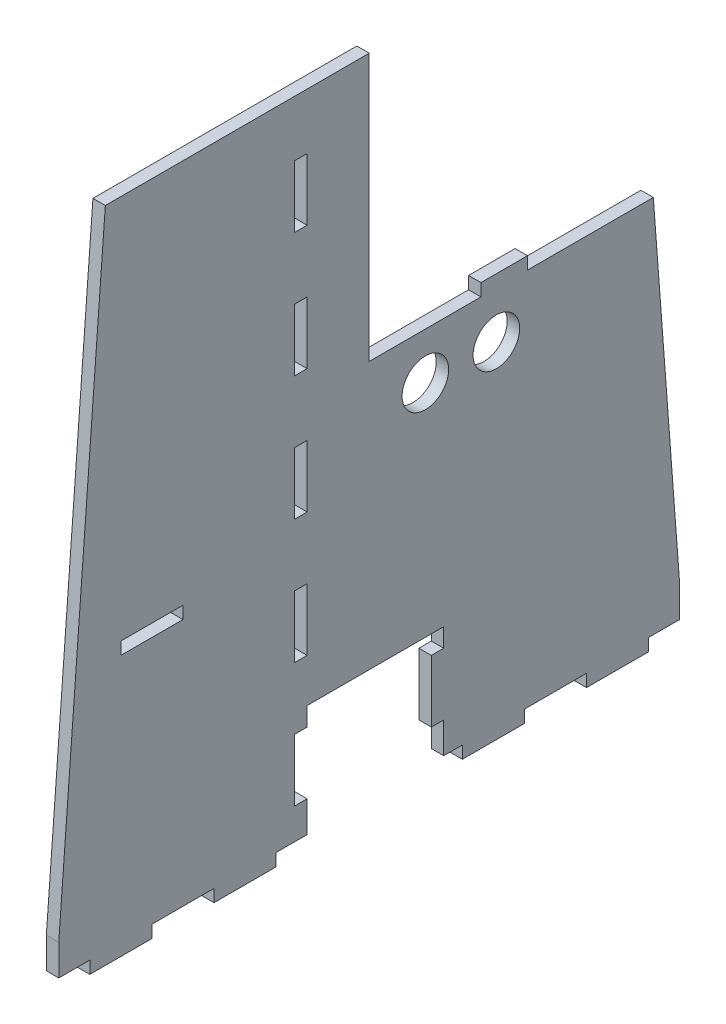
SolidWorks part; units mm, degrees
ref_plane "Přední rovina" through (0, 0, 0) normal (0, 0, 1) x (1, 0, 0)
ref_plane "Horní rovina" through (0, 0, 0) normal (0, 1, 0) x (1, 0, 0)
ref_plane "Pravá rovina" through (0, 0, 0) normal (1, 0, 0) x (0, 0, -1)
sketch "Skica1" plane through (0, 0, 0) normal (1, 0, 0) x (0, 0, -1)
  line L0 (0, 0) -> (0, 200)
  line L1 (-100, 0) -> (100, 0)
  line L2 (-100, 0) -> (-100, 212)
  line L3 (-100, 212) -> (100, 212)
  line L4 (100, 0) -> (100, 212)
  line L5 (-90, 0) -> (-70, 0)
  line L6 (-90, 0) -> (-90, 4)
  line L7 (-90, 4) -> (-70, 4)
  line L8 (-70, 0) -> (-70, 4)
  line L9 (-50, 0) -> (-30, 0)
  line L10 (-50, 0) -> (-50, 4)
  line L11 (-50, 4) -> (-30, 4)
  line L12 (-30, 0) -> (-30, 4)
  line L13 (-10, 0) -> (10, 0)
  line L17 (50, 4) -> (30, 4)
  line L18 (30, 0) -> (30, 4)
  line L19 (50, 0) -> (30, 0)
  line L20 (50, 0) -> (50, 4)
  line L21 (90, 4) -> (70, 4)
  line L22 (70, 0) -> (70, 4)
  line L23 (90, 0) -> (70, 0)
  line L24 (90, 0) -> (90, 4)
  line L25 (-8.5, 37) -> (0, 37)
  line L26 (0, 200) -> (0, 212)
  line L27 (-20, 14) -> (-24, 14)
  line L28 (-20, 14) -> (-20, 34)
  line L29 (-20, 34) -> (-24, 34)
  line L30 (-24, 14) -> (-24, 34)
  line L31 (-20, 54) -> (-24, 54)
  line L32 (-20, 54) -> (-20, 74)
  line L33 (-20, 74) -> (-24, 74)
  line L34 (-24, 54) -> (-24, 74)
  line L35 (-20, 94) -> (-24, 94)
  line L36 (-20, 94) -> (-20, 114)
  line L37 (-20, 114) -> (-24, 114)
  line L38 (-24, 94) -> (-24, 114)
  line L39 (-20, 134) -> (-24, 134)
  line L40 (-20, 134) -> (-20, 154)
  line L41 (-20, 154) -> (-24, 154)
  line L42 (-24, 134) -> (-24, 154)
  line L43 (-20, 174) -> (-24, 174)
  line L44 (-20, 174) -> (-20, 194)
  line L45 (-20, 194) -> (-24, 194)
  line L46 (-24, 174) -> (-24, 194)
  line L47 (-85, 212) -> (-100, 14)
  line L48 (100, 14) -> (85, 212)
  line L49 (91.5152, 126) -> (0, 126)
  line L51 (36, 126) -> (51, 126)
  line L52 (36, 126) -> (36, 130)
  line L53 (36, 130) -> (51, 130)
  line L54 (51, 126) -> (51, 130)
  line L57 (-100, 4) -> (-90, 4)
  line L58 (-70, 4) -> (-50, 4)
  line L59 (-30, 4) -> (-20, 4)
  line L60 (30, 4) -> (24, 4)
  line L61 (50, 4) -> (70, 4)
  line L62 (90, 4) -> (100, 4)
  line L64 (-20, 40) -> (24, 40)
  line L65 (-20, 40) -> (-20, 0)
  line L66 (-20, 0) -> (24, 0)
  line L67 (24, 40) -> (24, 0)
  line L68 (-20, 40) -> (24, 0) construction
  line L69 (-20, 0) -> (24, 40) construction
  line L70 (24, 34) -> (20, 34)
  line L71 (24, 34) -> (24, 14)
  line L72 (24, 14) -> (20, 14)
  line L73 (20, 34) -> (20, 14)
  line L74 (-80, 88) -> (-60, 88)
  line L75 (-80, 88) -> (-80, 84)
  line L76 (-80, 84) -> (-60, 84)
  line L77 (-60, 88) -> (-60, 84)
  circle A3 centre (18.0923, 111) radius 7.5
  circle A4 centre (40.9523, 111) radius 7.5
  point P20 (-70, 2)
  point P21 (-80, 4)
  point P56 (-22, 174)
  point P57 (-85, 212)
  point P59 (85, 212)
  point P82 (2, 20)
  dimension "D13" = 4
  dimension "D15" = 20
  dimension "D31" = 15
  dimension "D33" = 8
  dimension "D37" = 18.0923
  dimension "D7" = 10
  dimension "D1" = 200
  dimension "D2" = 100
  dimension "D3" = 212
  dimension "D5" = 0
  dimension "D6" = 20
  dimension "D8" = 20
  dimension "D9" = 20
  dimension "D10" = 4
  dimension "D11" = 0
  dimension "D12" = 0
  dimension "D14" = 8.5
  dimension "D16" = 37
  dimension "D17" = 10
  dimension "D18" = 20
  dimension "D19" = 20
  dimension "D20" = 20
  dimension "D21" = 20
  dimension "D22" = 20
  dimension "D23" = 20
  dimension "D24" = 20
  dimension "D25" = 20
  dimension "D26" = 20
  dimension "D27" = 4
  dimension "D28" = 20
  dimension "D29" = 85
  dimension "D30" = 22.86
  dimension "D32" = 74
  dimension "D34" = 36
  dimension "D35" = 15
  dimension "D36" = 111.5152
  dimension "D41" = 4
  dimension "D42" = 40
  dimension "D43" = 44
  dimension "D44" = 20
  dimension "D45" = 61
  dimension "D46" = 4
  dimension "D47" = 20
  dimension "D48" = 80
  dimension "D49" = 60
extrude "Přidat vysunutím1" add sketch "Skica1" along normal blind 4
